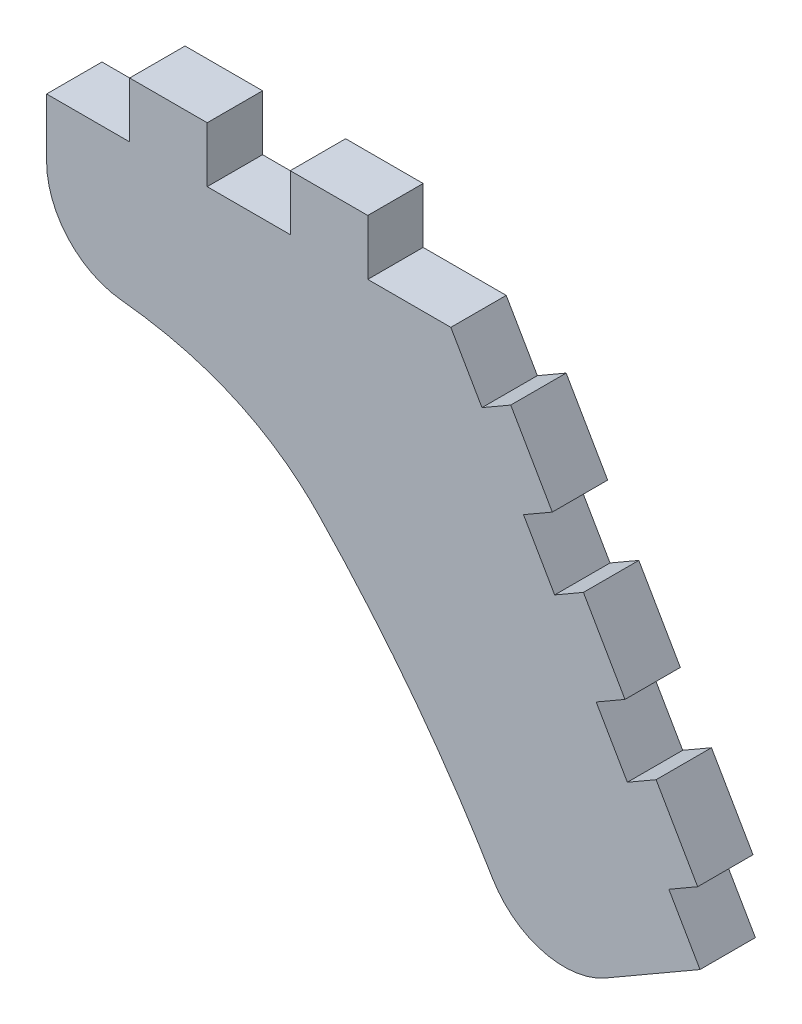
SolidWorks part; units mm, degrees
ref_plane "Front Plane" through (0, 0, 0) normal (0, 0, 1) x (1, 0, 0)
ref_plane "Top Plane" through (0, 0, 0) normal (0, 1, 0) x (1, 0, 0)
ref_plane "Right Plane" through (0, 0, 0) normal (1, 0, 0) x (0, 0, -1)
sketch "Sketch1" plane through (0, 0, 0) normal (0, 0, 1) x (1, 0, 0)
  line L0 (0, 0) -> (15, 0)
  line L1 (15, 0) -> (15, 10)
  line L2 (15, 10) -> (29, 10)
  line L3 (29, 10) -> (29, 0)
  line L4 (29, 0) -> (44, 0)
  line L5 (44, 0) -> (44, 10)
  line L6 (44, 10) -> (58, 10)
  line L7 (58, 10) -> (58, 0)
  line L8 (58, 0) -> (73, 0)
  line L9 (73, 0) -> (78.625, -9.7428)
  line L10 (78.625, -9.7428) -> (83.8212, -6.7428)
  line L11 (83.8212, -6.7428) -> (91.3212, -19.7332)
  line L12 (91.3212, -19.7332) -> (86.125, -22.7332)
  line L13 (86.125, -22.7332) -> (91.75, -32.476)
  line L14 (91.75, -32.476) -> (96.9462, -29.476)
  line L15 (96.9462, -29.476) -> (104.4462, -42.4663)
  line L16 (104.4462, -42.4663) -> (99.25, -45.4663)
  line L17 (99.25, -45.4663) -> (104.875, -55.2091)
  line L18 (104.875, -55.2091) -> (110.0712, -52.2091)
  line L19 (110.0712, -52.2091) -> (117.5712, -65.1995)
  line L20 (117.5712, -65.1995) -> (112.375, -68.1995)
  line L21 (112.375, -68.1995) -> (118, -77.9423)
  line L22 (118, -77.9423) -> (87.6891, -95.4423)
  line L23 (0, 0) -> (0, -25)
  line L24 (73, 0) -> (49.1605, -41.2913) construction
  spline S0 degree 3 poles (0, -25) (17.2425, -24.6396) (35.9, -27.5043) (49.1605, -41.2913) knots 0 0 0 0 1 1 1 1
  spline S1 degree 3 poles (87.6891, -95.4423) (77.6602, -75.62) (64.8173, -57.5697) (49.1605, -41.2913) knots 0 0 0 0 1 1 1 1
  dimension "D1" = 120
  dimension "D2" = 15
  dimension "D3" = 14
  dimension "D4" = 11.25
  dimension "D5" = 10
  dimension "D6" = 15
  dimension "D7" = 6
  dimension "D8" = 25
  dimension "D9" = 35
  dimension "D10" = 60
  dimension "D11" = 47.679
extrude "Boss-Extrude1" add sketch "Sketch1" along normal blind 10
fillet "Fillet1" radius 15 2 edges at (87.6891, -95.4423, 5) (0, -25, 5)
